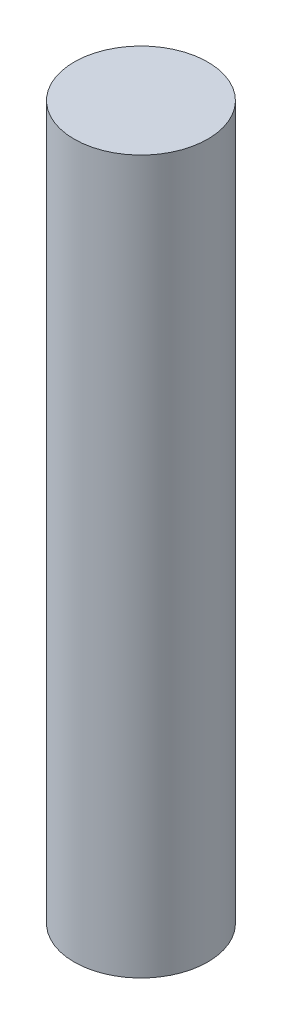
SolidWorks part; units mm, degrees
ref_plane "Front Plane" through (0, 0, 0) normal (0, 0, 1) x (1, 0, 0)
ref_plane "Top Plane" through (0, 0, 0) normal (0, 1, 0) x (1, 0, 0)
ref_plane "Right Plane" through (0, 0, 0) normal (1, 0, 0) x (0, 0, -1)
sketch "Sketch1" plane through (0, 0, 0) normal (0, 1, 0) x (1, 0, 0)
  circle A0 centre (0, 0) radius 0.75
  dimension "D1" = 1.5
extrude "Boss-Extrude1" add sketch "Sketch1" along normal blind 8
